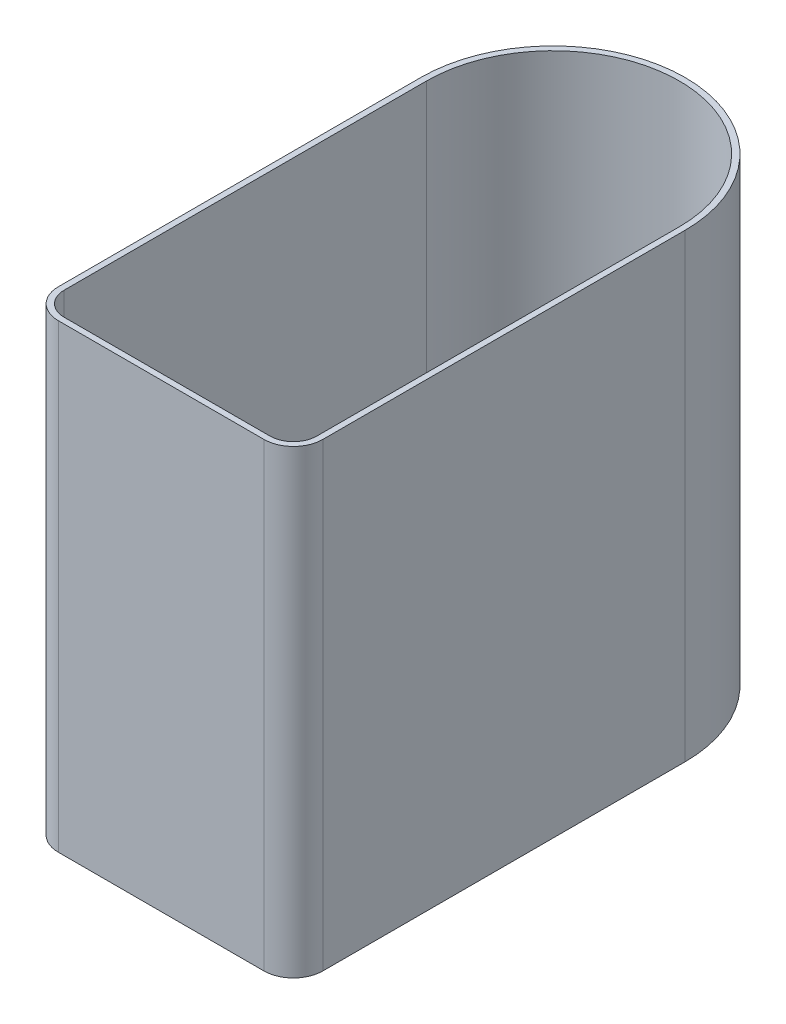
SolidWorks part; units mm, degrees
ref_plane "Front Plane" through (0, 0, 0) normal (0, 0, 1) x (1, 0, 0)
ref_plane "Top Plane" through (0, 0, 0) normal (0, 1, 0) x (1, 0, 0)
ref_plane "Right Plane" through (0, 0, 0) normal (1, 0, 0) x (0, 0, -1)
sketch "Sketch1" plane through (0, 0, 0) normal (0, 1, 0) x (1, 0, 0)
  line L0 (0, 0) -> (0, 100) construction
  line L1 (52.5, -100) -> (-52.5, -100)
  line L2 (67.5, -85) -> (67.5, 100)
  line L4 (-67.5, -85) -> (-67.5, 100)
  line L5 (67.5, -100) -> (-67.5, 100) construction
  line L6 (67.5, 100) -> (-67.5, -100) construction
  arc A0 (67.5, 100) -> (-67.5, 100) centre (0, 100) ccw
  arc A1 (52.5, -100) -> (67.5, -85) centre (52.5, -85) ccw
  arc A2 (-52.5, -100) -> (-67.5, -85) centre (-52.5, -85) cw
  point P0 (0, 0)
  point P9 (0, 0)
  point P10 (0, 0)
  point P11 (0, 0)
  dimension "D3" = 15
  dimension "D1" = 200
  dimension "D2" = 135
extrude "Boss-Extrude1" add sketch "Sketch1" along normal blind 235 contours L4 A0 L2 A1 L1 A2
shell "Shell1" thickness 3
